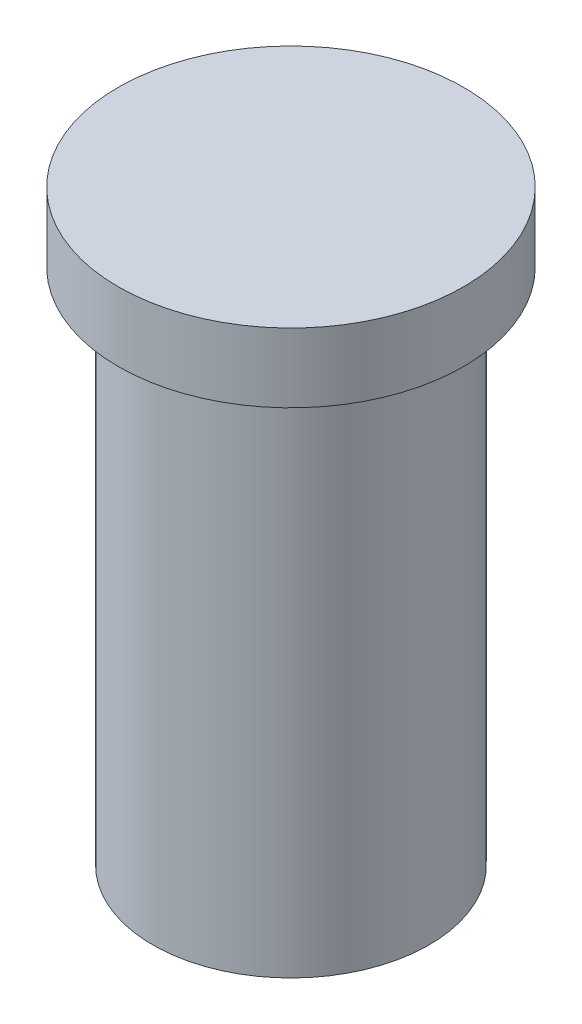
SolidWorks part; units mm, degrees
ref_plane "Front Plane" through (0, 0, 0) normal (0, 0, 1) x (1, 0, 0)
ref_plane "Top Plane" through (0, 0, 0) normal (0, 1, 0) x (1, 0, 0)
ref_plane "Right Plane" through (0, 0, 0) normal (1, 0, 0) x (0, 0, -1)
sketch "Sketch1" plane through (0, 0, 0) normal (0, 1, 0) x (1, 0, 0)
  circle A0 centre (0, 0) radius 5
  dimension "D1" = 10
extrude "Boss-Extrude1" add sketch "Sketch1" along normal blind 2
sketch "Sketch6" plane through (0, 0, 0) normal (0, -1, 0) x (-1, 0, 0)
  circle A0 centre (0, 0) radius 4
  dimension "D1" = 8
extrude "Boss-Extrude4" add sketch "Sketch6" along normal blind 15
